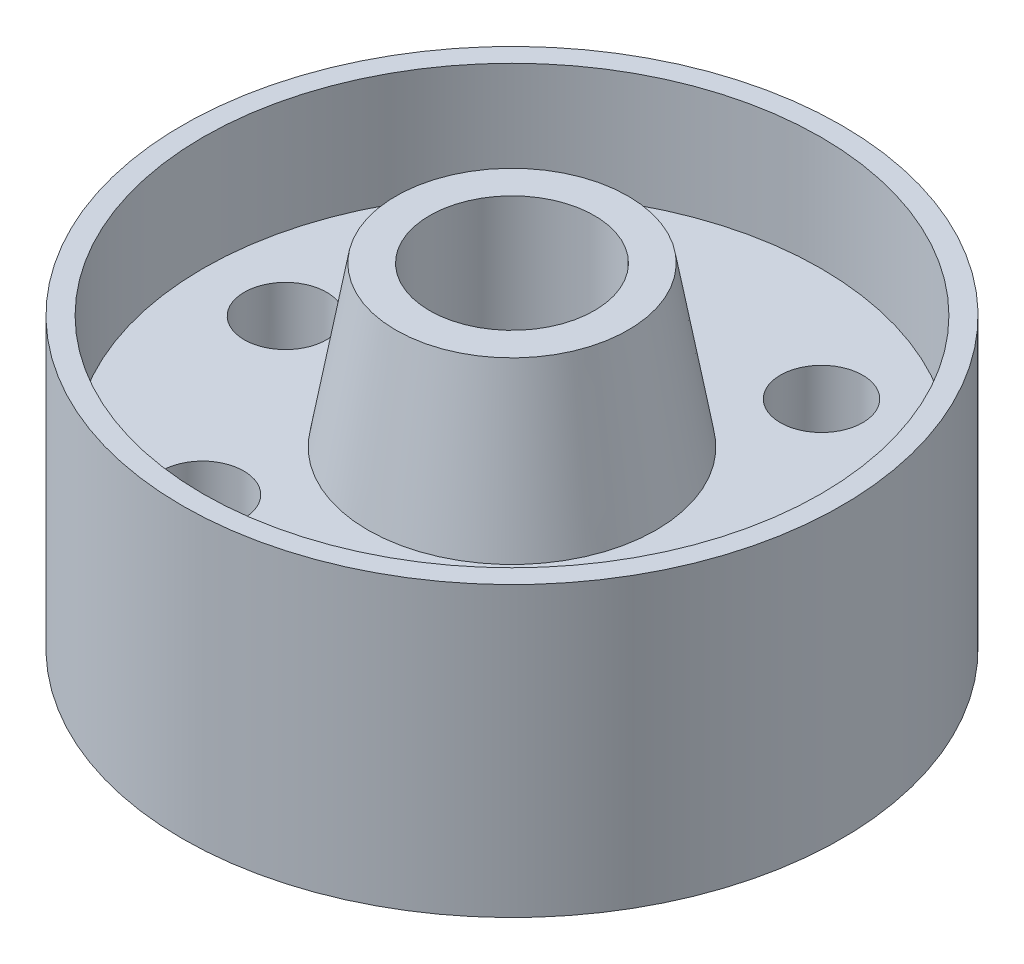
SolidWorks part; units mm, degrees
material "Plain Carbon Steel"
ref_plane "Front" through (0, 0, 0) normal (0, 0, 1) x (1, 0, 0)
ref_plane "Top" through (0, 0, 0) normal (0, 1, 0) x (1, 0, 0)
ref_plane "Right" through (0, 0, 0) normal (1, 0, 0) x (0, 0, -1)
sketch "Sketch1" plane through (0, 0, 0) normal (0, 0, 1) x (1, 0, 0)
  line L0 (0, 29.3497) -> (0, -29.3497) construction
  line L1 (-12.7, 29.3497) -> (-17.9008, 29.3497)
  line L2 (-17.9008, 29.3497) -> (-22.225, 4.826)
  line L3 (-22.225, 4.826) -> (-47.625, 4.826)
  line L4 (-47.625, 4.826) -> (-47.625, 22.352)
  line L5 (-47.625, 22.352) -> (-50.8, 22.352)
  line L6 (-50.8, 22.352) -> (-50.8, -22.098)
  line L7 (-50.8, -22.098) -> (-47.625, -22.098)
  line L8 (-47.625, -22.098) -> (-47.625, -4.826)
  line L9 (-47.625, -4.826) -> (-22.225, -4.826)
  line L10 (-22.225, -4.826) -> (-17.9008, -29.3497)
  line L11 (-17.9008, -29.3497) -> (-12.7, -29.3497)
  line L12 (-12.7, -29.3497) -> (-12.7, 29.3497)
  line L13 (17.9008, 29.3497) -> (22.225, 4.826) construction
  point P13 (0, 0)
  point P18 (0, 0)
  point P19 (0, 0)
  point P20 (-22.225, -5.0005)
  point P21 (-22.225, 4.6671)
  point P22 (0, 0)
  dimension "D1" = 20
  dimension "D2" = 17.526
  dimension "D3" = 9.652
  dimension "D4" = 101.6
  dimension "D5" = 95.25
  dimension "D6" = 44.45
  dimension "D7" = 25.4
  dimension "D8" = 44.45
  dimension "D9" = 58.6994
  dimension "D10" = 10
revolve "Revolve1" add sketch "Sketch1" angle 360 about L0
hole_wizard "1/2 (0.5) Diameter Hole1" positions "Sketch2" profile "Sketch3" hole size "1/2" standard "ANSI Inch" end condition through all
sketch "Sketch2" plane through (0, 4.826, 0) normal (0, 1, 0) x (1, 0, 0)
  line L0 (-17.4625, 30.2459) -> (17.4625, 30.2459) construction
  line L1 (17.4625, 30.2459) -> (34.925, 0) construction
  line L2 (34.925, 0) -> (17.4625, -30.2459) construction
  line L3 (17.4625, -30.2459) -> (-17.4625, -30.2459) construction
  line L4 (-17.4625, -30.2459) -> (-34.925, 0) construction
  line L5 (-34.925, 0) -> (-17.4625, 30.2459) construction
  circle A0 centre (0, 0) radius 34.925 construction
  point P0 (-17.4625, 30.2459)
  point P2 (17.4625, 30.2459)
  point P4 (-34.925, 0)
  point P6 (34.925, 0)
  point P8 (-17.4625, -30.2459)
  point P10 (17.4625, -30.2459)
  point P30 (0, 0)
  dimension "D1" = 69.85
sketch "Sketch3" plane through (-17.4625, 4.826, -30.2459) normal (1, 0, 0) x (0, 0, 1)
  line L0 (0, 0) -> (0, 34.1757)
  line L1 (0, 34.1757) -> (6.35, 34.1757)
  line L2 (6.35, 34.1757) -> (6.35, 0)
  line L5 (6.35, 0) -> (0, 0)
  line L11 (0, -6.35) -> (0, 107.95) construction
  dimension "Thru Hole Dia." = 12.7
  dimension "Thru Hole Depth" = 34.1757
